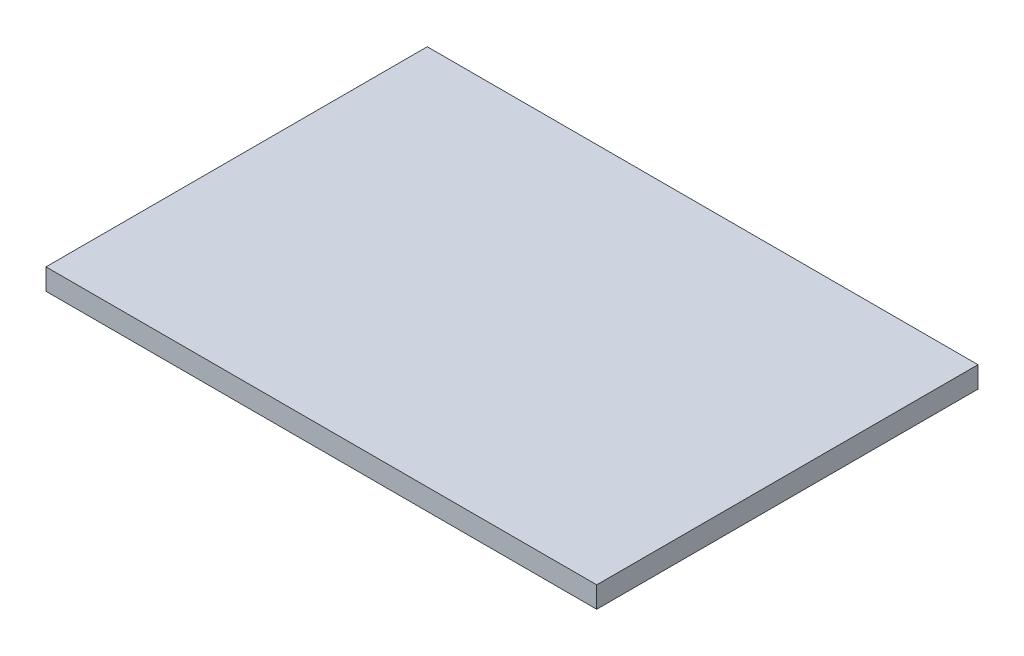
SolidWorks part; units mm, degrees
ref_plane "Front Plane" through (0, 0, 0) normal (0, 0, 1) x (1, 0, 0)
ref_plane "Top Plane" through (0, 0, 0) normal (0, 1, 0) x (1, 0, 0)
ref_plane "Right Plane" through (0, 0, 0) normal (1, 0, 0) x (0, 0, -1)
sketch "Sketch1" plane through (0, 0, 0) normal (0, 1, 0) x (1, 0, 0)
  line L1 (-13, -9) -> (13, -9)
  line L2 (-13, -9) -> (-13, 9)
  line L3 (-13, 9) -> (13, 9)
  line L4 (13, -9) -> (13, 9)
  line L5 (-13, -9) -> (13, 9) construction
  line L6 (-13, 9) -> (13, -9) construction
  point P0 (0, 0)
  dimension "D1" = 18
  dimension "D2" = 26
extrude "Boss-Extrude1" add sketch "Sketch1" along normal blind 1
